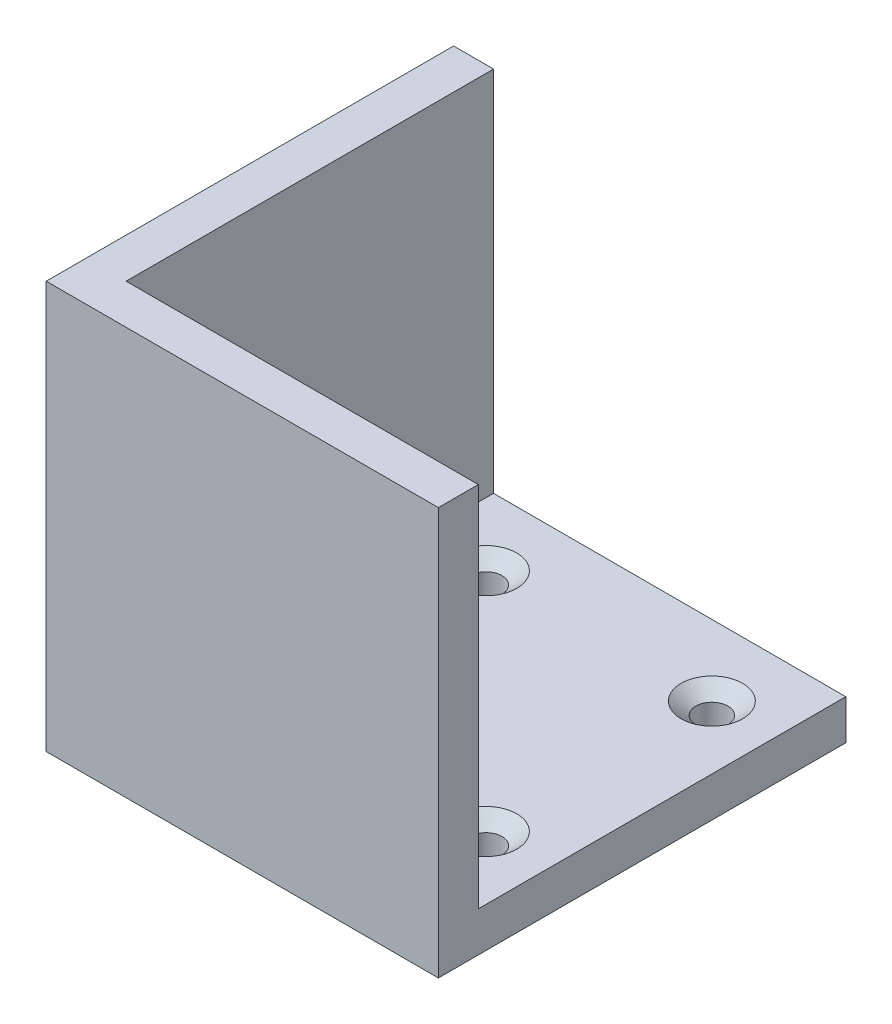
SolidWorks part; units mm, degrees
material "6061-T6 (SS)"
ref_plane "Front Plane" through (0, 0, 0) normal (0, 0, 1) x (1, 0, 0)
ref_plane "Top Plane" through (0, 0, 0) normal (0, 1, 0) x (1, 0, 0)
ref_plane "Right Plane" through (0, 0, 0) normal (1, 0, 0) x (0, 0, -1)
sketch "MotorProfile" plane through (0, 0, 0) normal (0, 1, 0) x (1, 0, 0)
  line L1 (-28, -29.21) -> (28, -29.21)
  line L2 (-28, -29.21) -> (-28, 29.21)
  line L3 (-28, 29.21) -> (28, 29.21)
  line L4 (28, -29.21) -> (28, 29.21)
  line L5 (-28, -29.21) -> (28, 29.21) construction
  line L6 (-28, 29.21) -> (28, -29.21) construction
  point P0 (0, 0)
  dimension "D1" = 56
  dimension "D2" = 58.42
sketch "Sketch2" plane through (0, 0, 0) normal (0, 1, 0) x (1, 0, 0)
  line L0 (-34.35, 29.21) -> (-34.35, -35.56)
  line L5 (-34.35, -35.56) -> (28, -35.56)
  line L6 (-28, -29.21) -> (-28, 29.21) construction
  line L7 (-34.35, 29.21) -> (-28, 29.21)
  line L8 (-28, 29.21) -> (-28, -29.21)
  line L9 (-28, -29.21) -> (28, -29.21)
  line L13 (28, -29.21) -> (28, -35.56)
  dimension "D1" = 6.35
  dimension "D2" = 6.35
  dimension "D3" = 28
  dimension "D4" = 29.21
sketch "Sketch3" plane through (0, 0, 0) normal (0, 1, 0) x (1, 0, 0)
  line L0 (17.9605, -17.9605) -> (-17.9605, 17.9605)
  line L1 (-17.9605, 17.9605) -> (-17.9605, -45.5395)
  line L2 (-17.9605, -45.5395) -> (53.8815, -45.5395)
  line L3 (17.9605, -17.9605) -> (53.8815, 17.9605)
  line L4 (53.8815, 17.9605) -> (53.8815, -45.5395)
  line L5 (0, 0) -> (104.1503, 0) construction
  point P4 (0, 0)
  dimension "D1" = 50.8
  dimension "D2" = 50.8
  dimension "D3" = 63.5
  dimension "D4" = 45
  dimension "D5" = 45
extrude "Boss-Extrude1" [suppressed] add sketch "Sketch3" along normal blind 50.8
extrude "Boss-Extrude2" add sketch "MotorProfile" along normal blind 6.35
extrude "Boss-Extrude3" add sketch "Sketch2" along normal blind 64.77
sketch "Sketch4" plane through (28, 0, 0) normal (1, 0, 0) x (0, 0, -1)
  line L1 (-35.56, 0) -> (29.21, 0)
  line L2 (-35.56, 0) -> (-35.56, 6.35)
  line L3 (-35.56, 6.35) -> (29.21, 6.35)
  line L4 (29.21, 0) -> (29.21, 6.35)
sketch "Sketch7" plane through (0, 6.35, 0) normal (0, 1, 0) x (1, 0, 0)
  line L0 (0, 0) -> (-17.9605, 17.9605) construction
  line L1 (0, 0) -> (0, 52.0192) construction
  line L2 (0, 0) -> (55.2901, 0) construction
  point P0 (-17.9605, 17.9605)
  point P1 (0, 0)
  point P2 (0, 0)
  point P3 (0, 0)
  point P6 (0, 0)
  point P10 (0, 0)
  point P11 (44.3962, 24.5988)
  point P12 (17.9605, 17.9605)
  point P13 (-17.9605, -17.9605)
  point P14 (17.9605, -17.9605)
  dimension "D1" = 25.4
hole_wizard "CSK for #10 Flat Head Machine Screw (100)1" positions "Sketch8" profile "Sketch9" countersink size "#10" standard "ANSI Inch" end condition through all
sketch "Sketch8" plane through (0, 6.35, 0) normal (0, 1, 0) x (1, 0, 0)
  point P0 (-17.9605, 17.9605)
  point P3 (-17.9605, -17.9605)
  point P6 (17.9605, -17.9605)
  point P9 (17.9605, 17.9605)
sketch "Sketch9" plane through (-17.9605, 6.35, -17.9605) normal (1, 0, 0) x (0, 0, 1)
  line L0 (0, 0) -> (0, 6.35)
  line L1 (0, 6.35) -> (2.5527, 6.35)
  line L2 (2.5527, 6.35) -> (2.5527, 1.9608)
  line L3 (2.5527, 1.9608) -> (4.8895, 0)
  line L5 (4.8895, 0) -> (0, 0)
  line L6 (-2.5527, 1.9608) -> (-4.8895, 0) construction
  line L11 (0, -6.35) -> (0, 107.95) construction
  dimension "Thru Hole Dia." = 5.1054
  dimension "Thru Hole Depth" = 6.35
  dimension "Near C'Sink Dia." = 9.779
  dimension "Near C'Sink Angle" = 100
equation "\"1n\"=0.5"
